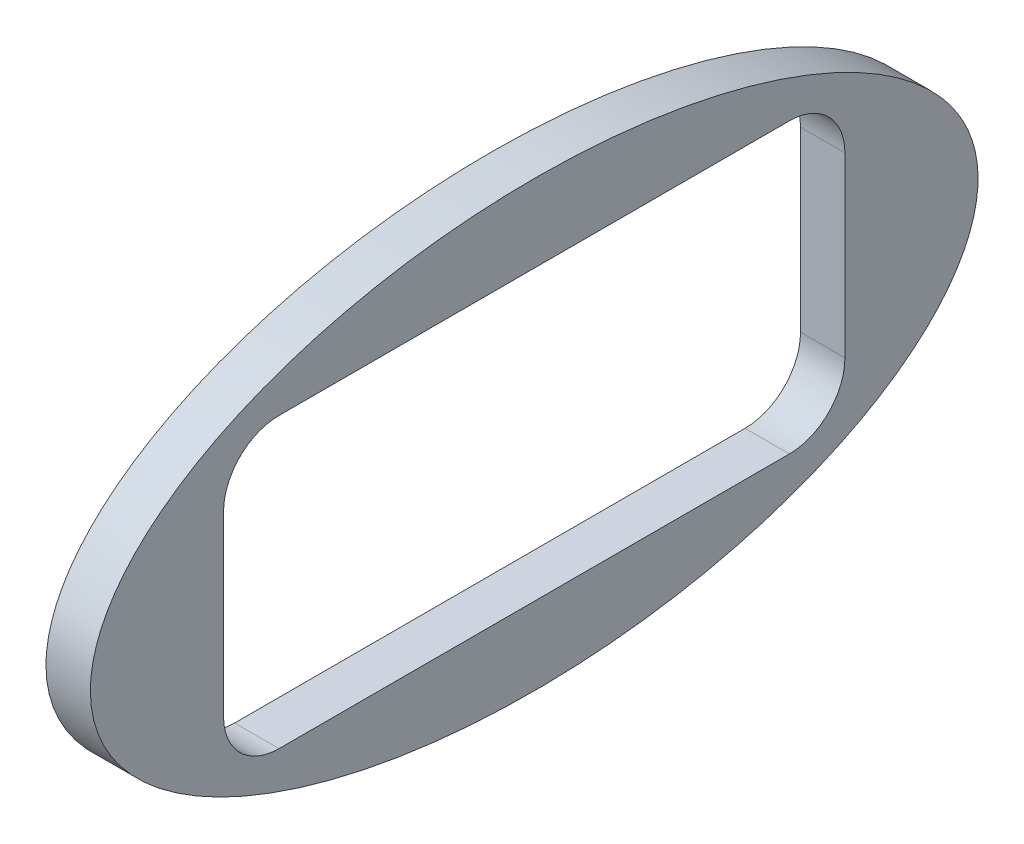
SolidWorks part; units mm, degrees
ref_plane "Front Plane" through (0, 0, 0) normal (0, 0, 1) x (1, 0, 0)
ref_plane "Top Plane" through (0, 0, 0) normal (0, 1, 0) x (1, 0, 0)
ref_plane "Right Plane" through (0, 0, 0) normal (1, 0, 0) x (0, 0, -1)
other "Configuration Table"
sketch "Outer_sketch" plane through (0, 0, 0) normal (1, 0, 0) x (0, 0, -1)
  line L1 (-6, -2.25) -> (6, -2.25) construction
  line L2 (-6, -2.25) -> (-6, 2.25) construction
  line L3 (-6, 2.25) -> (6, 2.25) construction
  line L4 (6, -2.25) -> (6, 2.25) construction
  line L5 (-6, -2.25) -> (6, 2.25) construction
  line L6 (-6, 2.25) -> (6, -2.25) construction
  ellipse E0 centre (0, 0) end of major axis (-10, 0) minor radius 5
  dimension "D1" = 12
  dimension "D2" = 4.5
  dimension "D3" = 10
  dimension "D4" = 20
sketch "Hole_sketch" plane through (0, 0, 0) normal (1, 0, 0) x (0, 0, -1)
  line L0 (-7, -2) -> (-7, 2)
  line L1 (-5.75, -2.25) -> (5.75, -2.25) construction
  line L2 (-6, -2) -> (-6, 2) construction
  line L3 (-5.75, 2.25) -> (5.75, 2.25) construction
  line L4 (6, -2) -> (6, 2) construction
  line L5 (-6, -2.25) -> (6, 2.25) construction
  line L6 (-6, 2.25) -> (6, -2.25) construction
  line L7 (-5.75, 3.25) -> (5.75, 3.25)
  line L8 (7, -2) -> (7, 2)
  line L9 (-5.75, -3.25) -> (5.75, -3.25)
  arc A0 (5.75, 2.25) -> (6, 2) centre (5.75, 2) cw construction
  arc A1 (5.75, -2.25) -> (6, -2) centre (5.75, -2) ccw construction
  arc A2 (-5.75, -2.25) -> (-6, -2) centre (-5.75, -2) cw construction
  arc A3 (-6, 2) -> (-5.75, 2.25) centre (-5.75, 2) cw construction
  arc A4 (-7, 2) -> (-5.75, 3.25) centre (-5.75, 2) cw
  arc A5 (5.75, 3.25) -> (7, 2) centre (5.75, 2) cw
  arc A6 (5.75, -3.25) -> (7, -2) centre (5.75, -2) ccw
  arc A7 (-5.75, -3.25) -> (-7, -2) centre (-5.75, -2) cw
  point P0 (0, 0)
  dimension "D3" = 0.25
  dimension "D1" = 12
  dimension "D2" = 4.5
  dimension "D4" = 1
extrude "LED_body" add sketch "Outer_sketch" along normal blind 1
extrude "LED_surface" cut sketch "Hole_sketch" along normal through all
